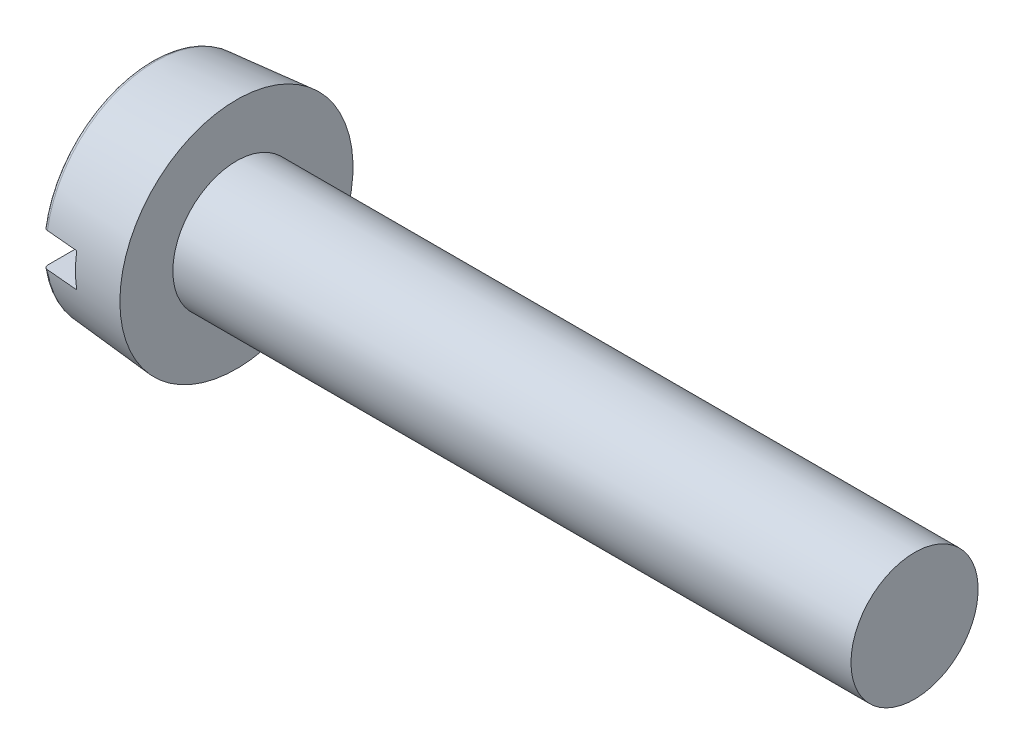
SolidWorks part; units mm, degrees
ref_plane "Plane1" through (0, 0, 0) normal (0, 0, 1) x (1, 0, 0)
ref_plane "Plane2" through (0, 0, 0) normal (0, 1, 0) x (1, 0, 0)
ref_plane "Plane3" through (0, 0, 0) normal (1, 0, 0) x (0, 0, -1)
sketch "BodySke" plane through (0, 0, 0) normal (0, 0, 1) x (1, 0, 0)
  line L0 (2, 1.5) -> (2, 2.75)
  line L1 (0, 0) -> (0, 2.575)
  line L2 (-25.4, 0) -> (127, 0) construction
  line L3 (18, 0) -> (0, 0)
  line L4 (2, 1.5) -> (18, 1.5)
  line L5 (18, 1.5) -> (18, 0)
  line L6 (0, 2.575) -> (2, 2.75)
  line L9 (2.5, 3.0875) -> (2.5, -6.4375) construction
  line L10 (2, 6.35) -> (2, -3.175) construction
  dimension "Length" = 16
  dimension "Head_ht" = 2
  dimension "Advance" = 0.5
  dimension "Thread_nom" = 16
  dimension "Head_dia" = 5.5
  dimension "Head_side_angle" = 5
  dimension "Diameter" = 3
revolve "Base-Revolve" add sketch "BodySke"
cosmetic thread "ThreadCosmetic" [suppressed]
fillet "Fillet1" [suppressed] radius 0.1
fillet "Fillet2" radius 0.1 1 edges at (0, 0, 2.575)
sketch "Sketch2" plane through (0, 0, 0) normal (1, 0, 0) x (0, 0, -1)
  line L0 (2.75, -0.4) -> (-2.75, -0.4)
  line L1 (2.75, -0.4) -> (2.75, 0.4)
  line L2 (-2.75, 0.4) -> (2.75, 0.4)
  line L3 (-2.75, 0.4) -> (-2.75, -0.4)
  dimension "D1" = 5.5
  dimension "Slot_width" = 0.8
  dimension "D2" = 2.75
  dimension "D3" = 0.4
extrude "Slot" cut sketch "Sketch2" along normal blind 0.85
sketch "ThdSchSke" plane through (0, 0, 0) normal (0, 0, 1) x (1, 0, 0)
  line L0 (3, -1.2195) -> (2.8036, -1.5)
  line L1 (3, -1.2195) -> (3.1964, -1.5)
  line L2 (3.1964, -1.5) -> (3.1964, -1.875)
  line L3 (-3.175, 0) -> (5.1513, 0) construction
  line L5 (3.1964, -1.875) -> (2.8036, -1.875)
  line L6 (2.8036, -1.875) -> (2.8036, -1.5)
  dimension "Diameter" = 3
  dimension "SideAngle" = 55
  dimension "VeeAngle" = 70
  dimension "Thread_minor" = 2.439
  dimension "Overcut" = 3.75
  dimension "Start" = 3
revolve "ThreadSchematic" [suppressed] cut sketch "ThdSchSke" angle 360 about L3
pattern_linear "ThdSchPat" [suppressed]
equation "\"D1@Sketch2\" = \"Head_dia@BodySke\""
equation "\"D2@Sketch2\" = \"D1@Sketch2\" / 2"
equation "\"D3@Sketch2\" = \"Slot_width@Sketch2\" / 2"
equation "\"Thread_length@ThreadCosmetic\" = ((sgn( (\"Length@BodySke\" - \"Advance@BodySke\" * 2.0 ) - \"Thread_nom@BodySke\" )-1)*( (\"Length@BodySke\" - \"Advance@BodySke\"  * 2.0) - \"Thread_nom@BodySke\" ))/-2+ \"Thread_nom@BodySke\""
equation "\"Thread_minor@ThdSchSke\" = \"Thread_minor@ThreadCosmetic\""
equation "\"Diameter@ThdSchSke\" = \"Diameter@BodySke\""
equation "\"Overcut@ThdSchSke\" = \"Diameter@BodySke\" * 1.25"
equation "\"Start@ThdSchSke\" = \"Head_ht@BodySke\" + \"Length@BodySke\" - \"Thread_length@ThreadCosmetic\"  '---Non-countersunk---"
equation "\"Num_threads@ThdSchPat\" = int( \"Thread_length@ThreadCosmetic\" / \"Advance@BodySke\" + 0.999 )  + 1"
equation "\"Advance@ThdSchPat\" = \"Thread_length@ThreadCosmetic\" /  (\"Num_threads@ThdSchPat\" - 1) 'relax it"
